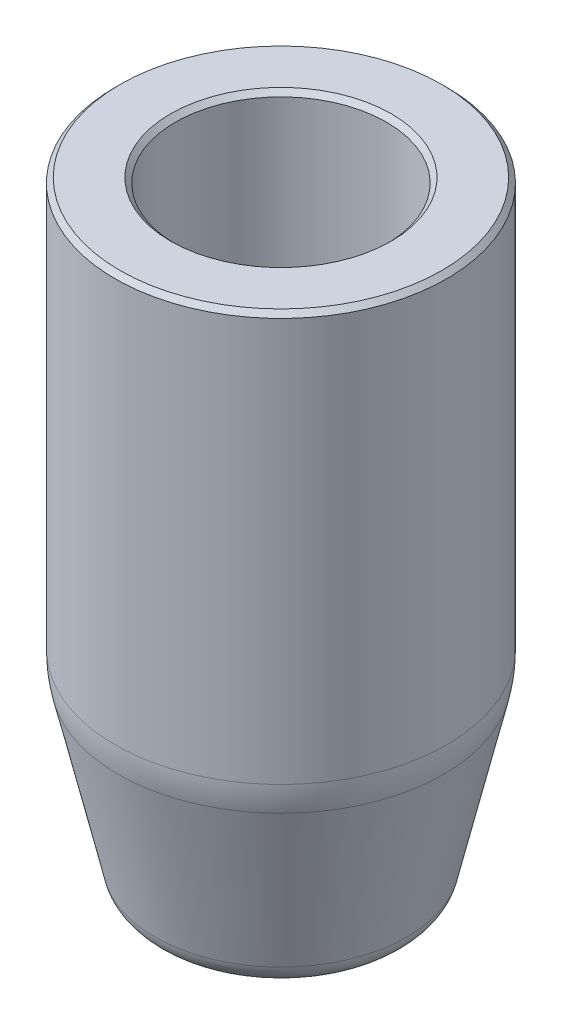
SolidWorks part; units mm, degrees
ref_plane "Front Plane" through (0, 0, 0) normal (0, 0, 1) x (1, 0, 0)
ref_plane "Top Plane" through (0, 0, 0) normal (0, 1, 0) x (1, 0, 0)
ref_plane "Right Plane" through (0, 0, 0) normal (1, 0, 0) x (0, 0, -1)
sketch "Sketch1" plane through (0, 0, 0) normal (0, 0, 1) x (1, 0, 0)
  line L0 (0, 4.298) -> (0, -4.298) construction
  line L3 (8.7312, 32.5437) -> (5.5562, 32.5437)
  line L4 (5.5562, 32.5437) -> (5.5563, 10.3188)
  line L5 (5.5563, 10.3188) -> (3.9687, 10.3188)
  line L6 (3.9687, 10.3188) -> (3.9688, 3.175)
  line L7 (3.9688, 3.175) -> (2.3813, 3.175)
  line L8 (2.3813, 3.175) -> (2.3813, 0)
  line L9 (8.7312, 32.5437) -> (8.7312, 10.3188)
  line L12 (6.35, 0) -> (8.7312, 10.3188)
  line L15 (2.3813, 0) -> (6.35, 0)
  dimension "D1" = 4.7625
  dimension "D2" = 3.175
  dimension "D3" = 7.9375
  dimension "D4" = 11.1125
  dimension "D5" = 12.7
  dimension "D6" = 7.1437
  dimension "D7" = 22.225
  dimension "D8" = 3.175
  dimension "D10" = 17.4625
revolve "Revolve1" add sketch "Sketch1" angle 360 about L0
fillet "Fillet2" radius 6.35 1 edges at (0, 10.3188, 8.7312)
fillet "Fillet3" radius 1.5875 1 edges at (0, 0, 6.35)
fillet "Fillet1" radius 0.7937 2 edges at (0, 10.3188, 5.5562) (0, 3.175, 3.9687)
chamfer "Chamfer1" distance 0.254 angle 45 5 edges at (0, 3.175, 2.3812) (0, 0, 2.3812) (0, 32.5437, 8.7312) (0, 32.5437, 5.5562) (0, 10.3188, 3.9687)
